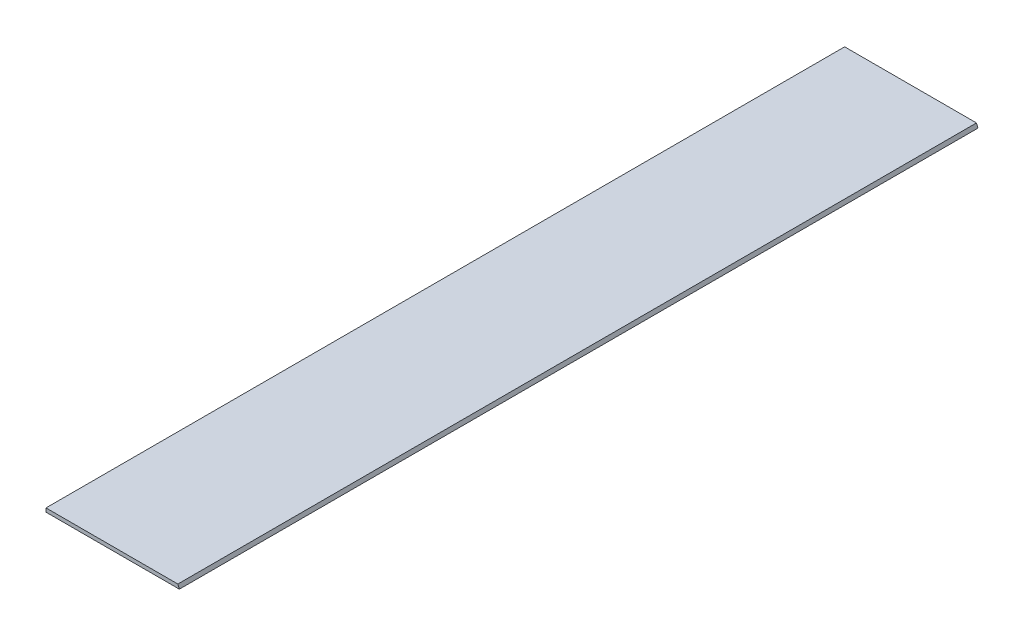
SolidWorks part; units mm, degrees
ref_plane "Front Plane" through (0, 0, 0) normal (0, 0, 1) x (1, 0, 0)
ref_plane "Top Plane" through (0, 0, 0) normal (0, 1, 0) x (1, 0, 0)
ref_plane "Right Plane" through (0, 0, 0) normal (1, 0, 0) x (0, 0, -1)
sketch "Sketch1" plane through (0, 0, 0) normal (0, 0, 1) x (1, 0, 0)
  line L0 (0, 0) -> (0, 2.3622)
  line L1 (0, 2.3622) -> (83.8575, 2.3622)
  line L2 (83.8575, 2.3622) -> (84.836, 0)
  line L3 (84.836, 0) -> (0, 0)
  dimension "D1" = 2.3622
  dimension "D2" = 67.5
  dimension "D3" = 84.836
extrude "Boss-Extrude1" add sketch "Sketch1" along normal blind 508
